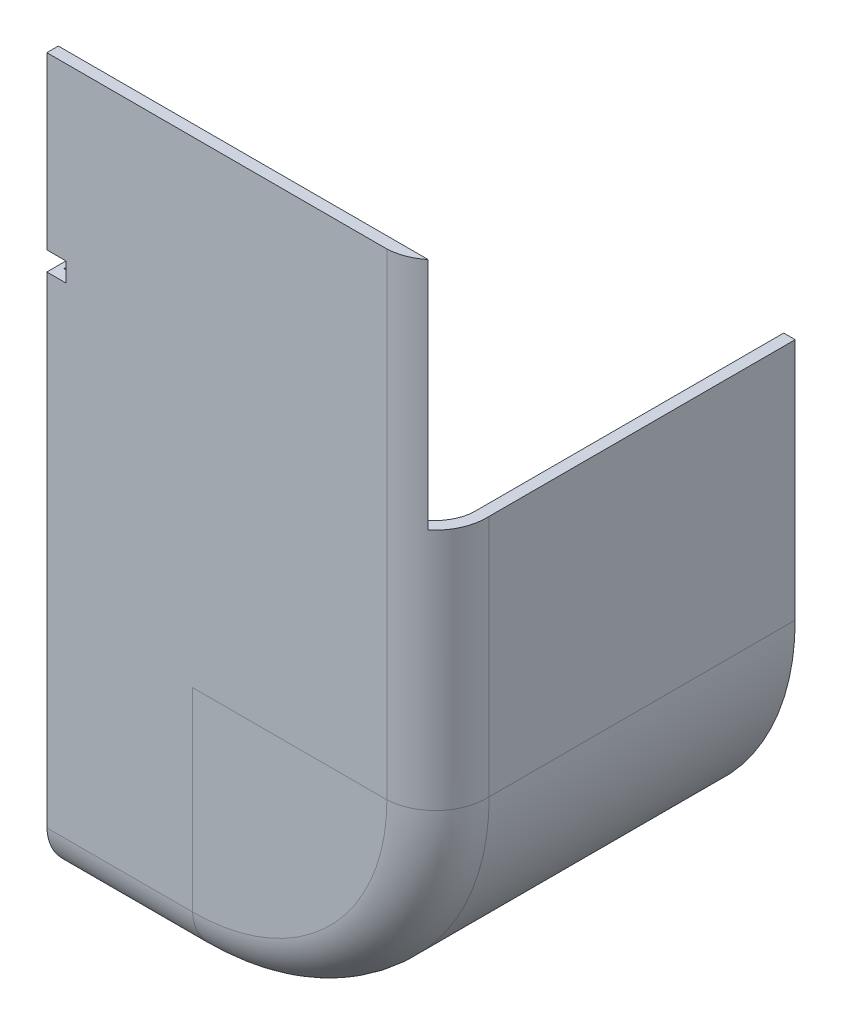
SolidWorks part; units mm, degrees
material "ABS"
ref_plane "Front Plane" through (0, 0, 0) normal (0, 0, 1) x (1, 0, 0)
ref_plane "Top Plane" through (0, 0, 0) normal (0, 1, 0) x (1, 0, 0)
ref_plane "Right Plane" through (0, 0, 0) normal (1, 0, 0) x (0, 0, -1)
sketch "Sketch1" plane through (0, 0, 0) normal (0, 0, 1) x (1, 0, 0)
  line L0 (-98.6, 98.6) -> (-98.6, -38.1)
  line L1 (-101.6, 101.6) -> (-101.6, -38.1)
  line L2 (-101.6, 101.6) -> (101.6, 101.6)
  line L3 (101.6, 101.6) -> (101.6, -38.1)
  line L4 (-38.1, -101.6) -> (38.1, -101.6)
  line L5 (-98.6, 98.6) -> (98.6, 98.6)
  line L6 (98.6, 98.6) -> (98.6, -38.1)
  line L7 (-38.1, -98.6) -> (38.1, -98.6)
  arc A0 (38.1, -101.6) -> (101.6, -38.1) centre (38.1, -38.1) ccw
  arc A1 (-101.6, -38.1) -> (-38.1, -101.6) centre (-38.1, -38.1) ccw
  arc A4 (98.6, -38.1) -> (38.1, -98.6) centre (38.1, -38.1) cw
  arc A5 (-38.1, -98.6) -> (-98.6, -38.1) centre (-38.1, -38.1) cw
  dimension "D5" = 63.5
  dimension "D6" = 63.5
  dimension "D1" = 203.2
  dimension "D2" = 139.7
  dimension "D3" = 139.7
  dimension "D4" = 76.2
  dimension "D7" = 101.6
  dimension "D8" = 101.6
  dimension "D9" = 3
  dimension "D10" = 3
  dimension "D11" = 3
  dimension "D12" = 3
  dimension "D13" = 0
  dimension "D14" = 0
  dimension "D15" = 0
  dimension "D16" = 0
extrude "Boss-Extrude1" add sketch "Sketch1" along normal blind 60 contours L1 A1 L4 A0 L3 L2 | L0 A5 L7 A4 L6 L5
sketch "Sketch3" plane through (0, 101.6, 0) normal (0, 1, 0) x (1, 0, 0)
  line L1 (-101.6, -60) -> (101.6, -60) construction
  line L2 (-38.1, -91.0391) -> (-88.9, -91.0391)
  line L3 (-98.6, -60) -> (-98.6, -80)
  line L4 (-38.1, -94.0391) -> (-38.1, -91.0391)
  line L7 (-98.6, -60) -> (-101.6, -60)
  line L9 (-101.6, -60) -> (-101.6, -80)
  line L10 (-38.1, -94.0391) -> (-88.9, -94.0391)
  arc A0 (-98.6, -80) -> (-88.9, -91.0391) centre (-88.0412, -80.5032) ccw
  arc A4 (-101.6, -80) -> (-88.9, -94.0391) centre (-88.2305, -80.6695) ccw
  dimension "D1" = 63.5
  dimension "D2" = 3
  dimension "D3" = 3
  dimension "D5" = 20
sketch "Sketch5" plane through (0, 0, 60) normal (0, 0, 1) x (1, 0, 0)
  line L0 (-100.1, 101.6) -> (-100.1, -38.1)
  line L1 (-98.6, 101.6) -> (-101.6, 101.6) construction
  line L2 (-101.6, 101.6) -> (-101.6, -38.1) construction
  line L3 (-38.1, -98.6) -> (-38.1, -101.6) construction
  line L4 (38.1, -98.6) -> (38.1, -101.6) construction
  line L5 (98.6, -38.1) -> (101.6, -38.1) construction
  line L6 (38.1, -100.1) -> (-38.1, -100.1)
  line L7 (100.1, -38.1) -> (100.1, 101.6)
  line L8 (-101.6, 101.6) -> (101.6, 101.6) construction
  arc A0 (-100.1, -38.1) -> (-38.1, -100.1) centre (-38.1, -38.1) ccw
  arc A1 (38.1, -100.1) -> (100.1, -38.1) centre (38.1, -38.1) ccw
  dimension "D1" = 0
  dimension "D2" = 1.5
  dimension "D3" = 0
sweep "Sweep2" add profiles "Sketch3" path "Sketch5"
sketch "Sketch6" plane through (0, 0, 94.0391) normal (0, 0, 1) x (1, 0, 0)
  line L0 (38.1, -38.1) -> (-38.1, -38.1)
  line L1 (-38.1, -38.1) -> (-38.1, 101.6)
  line L2 (-38.1, 101.6) -> (38.1, 101.6)
  line L3 (38.1, 101.6) -> (38.1, -38.1)
extrude "Boss-Extrude3" add sketch "Sketch6" against normal blind 3
sketch "Sketch7" plane through (0, 101.6, 0) normal (0, 1, 0) x (1, 0, 0)
  line L1 (122.4585, 44.29) -> (-132.2369, 44.29)
  line L2 (122.4585, 44.29) -> (122.4585, -91.0391)
  line L3 (122.4585, -91.0391) -> (-132.2369, -91.0391)
  line L4 (-132.2369, 44.29) -> (-132.2369, -91.0391)
  line L5 (122.4585, 44.29) -> (-132.2369, -91.0391) construction
  line L6 (122.4585, -91.0391) -> (-132.2369, 44.29) construction
  point P0 (-4.8892, -23.3746)
extrude "Cut-Extrude1" cut sketch "Sketch7" against normal blind 76.2
sketch "Sketch8" plane through (0, 0, 94.0391) normal (0, 0, 1) x (1, 0, 0)
  line L0 (0, 0) -> (0, 39.4405) construction
  line L2 (-5, 41.9405) -> (5, 41.9405)
  line L3 (-5, 41.9405) -> (-5, 36.9405)
  line L4 (-5, 36.9405) -> (5, 36.9405)
  line L5 (5, 41.9405) -> (5, 36.9405)
  line L6 (-5, 41.9405) -> (5, 36.9405) construction
  line L7 (-5, 36.9405) -> (5, 41.9405) construction
extrude "Cut-Extrude2" cut sketch "Sketch8" against normal through all
sketch "Sketch9" plane through (0, -101.6, 0) normal (0, -1, 0) x (-1, 0, 0)
  line L0 (38.1, 0) -> (-38.1, 0) construction
  line L1 (27.5, 0) -> (-27.5, 0)
  line L2 (27.5, 0) -> (27.5, -40)
  line L3 (27.5, -40) -> (-27.5, -40)
  line L4 (-27.5, 0) -> (-27.5, -40)
  line L5 (27.5, 0) -> (-27.5, -40) construction
  line L6 (27.5, -40) -> (-27.5, 0) construction
  line L7 (0, -20) -> (0, 0) construction
  point P0 (0, -20)
  dimension "D1" = 0
  dimension "D2" = 40
  dimension "D3" = 55
extrude "Cut-Extrude3" cut sketch "Sketch9" against normal through all
sketch "Sketch10" plane through (0, 101.6, 0) normal (0, 1, 0) x (1, 0, 0)
  line L0 (-88.9, -94.0391) -> (88.9, -94.0391) construction
  line L1 (100.3822, -101.2333) -> (-100.3822, -101.2333)
  line L2 (100.3822, -101.2333) -> (100.3822, -86.8449)
  line L3 (100.3822, -86.8449) -> (-100.3822, -86.8449)
  line L4 (-100.3822, -101.2333) -> (-100.3822, -86.8449)
  line L5 (100.3822, -101.2333) -> (-100.3822, -86.8449) construction
  line L6 (100.3822, -86.8449) -> (-100.3822, -101.2333) construction
  point P0 (0, -94.0391)
extrude "Cut-Extrude4" cut sketch "Sketch10" against normal blind 15
sketch "Sketch11" plane through (0, -98.6, 0) normal (0, 1, 0) x (1, 0, 0)
  line L0 (0, -40) -> (0, -80) construction
  line L1 (-27.5, -40) -> (27.5, -40) construction
  line L2 (-38.1, -80) -> (38.1, -80) construction
  line L3 (0, -80) -> (1.5, -80)
  line L4 (1.5, -80) -> (1.5, -40)
  line L5 (1.5, -40) -> (0, -40)
  line L6 (0, -80) -> (-1.5, -80)
  line L7 (-1.5, -80) -> (-1.5, -40)
  line L8 (-1.5, -40) -> (0, -40)
  dimension "D1" = 1.5
  dimension "D2" = 1.5
extrude "Boss-Extrude4" add sketch "Sketch11" along normal blind 4
sketch "Sketch12" plane through (0, 0, 91.0391) normal (0, 0, -1) x (-1, 0, 0)
  line L0 (0, -88.9) -> (0, 36.9405) construction
  line L1 (38.1, -88.9) -> (-38.1, -88.9) construction
  line L5 (-1.5, -88.9) -> (0, -88.9)
  line L6 (0, -88.9) -> (1.5, -88.9)
  line L7 (1.5, -88.9) -> (1.5, 36.9405)
  line L11 (-1.5, 36.9405) -> (1.5, 36.9405)
  line L12 (5, 36.9405) -> (-5, 36.9405) construction
  line L13 (-1.5, 36.9405) -> (-1.5, -88.9)
extrude "Boss-Extrude5" add sketch "Sketch12" along normal blind 4 contours L7 L11 L13 L5 L6
sketch "Sketch13" plane through (-101.6, 0, 0) normal (-1, 0, 0) x (0, 0, 1)
  line L1 (-56.7304, -154.7217) -> (106.0682, -154.7217)
  line L2 (-56.7304, -154.7217) -> (-56.7304, 92.0139)
  line L3 (-56.7304, 92.0139) -> (106.0682, 92.0139)
  line L4 (106.0682, -154.7217) -> (106.0682, 92.0139)
  line L5 (-56.7304, -154.7217) -> (106.0682, 92.0139) construction
  line L6 (-56.7304, 92.0139) -> (106.0682, -154.7217) construction
  point P0 (24.6689, -31.3539)
extrude "Cut-Extrude5" cut sketch "Sketch13" against normal blind 101.6
